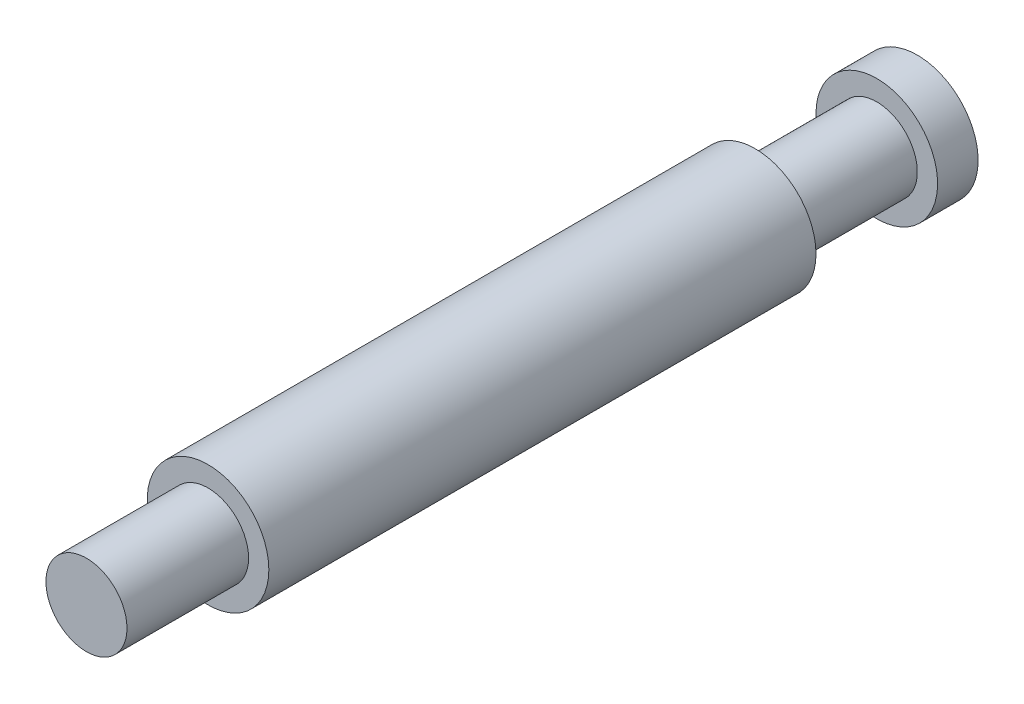
SolidWorks part; units mm, degrees
ref_plane "前视基准面" through (0, 0, 0) normal (0, 0, 1) x (1, 0, 0)
ref_plane "上视基准面" through (0, 0, 0) normal (0, 1, 0) x (1, 0, 0)
ref_plane "右视基准面" through (0, 0, 0) normal (1, 0, 0) x (0, 0, -1)
other "Configuration Table"
sketch "草图1" plane through (0, 0, 0) normal (0, 0, 1) x (1, 0, 0)
  circle A0 centre (0, 0) radius 1.5
  dimension "D1" = 3
extrude "凸台-拉伸1" add sketch "草图1" along normal blind 13.5
sketch "草图2" plane through (0, 0, 13.5) normal (0, 0, 1) x (1, 0, 0)
  circle A0 centre (0, 0) radius 1
  dimension "D1" = 2
extrude "凸台-拉伸2" add sketch "草图2" along normal blind 3
sketch "草图3" plane through (0, 0, 0) normal (0, 0, -1) x (-1, 0, 0)
  circle A0 centre (0, 0) radius 1
  dimension "D1" = 2
extrude "凸台-拉伸3" add sketch "草图3" along normal blind 3
sketch "草图4" plane through (0, 0, -3) normal (0, 0, -1) x (-1, 0, 0)
  circle A0 centre (0, 0) radius 1.5
extrude "凸台-拉伸4" add sketch "草图4" along normal blind 1
